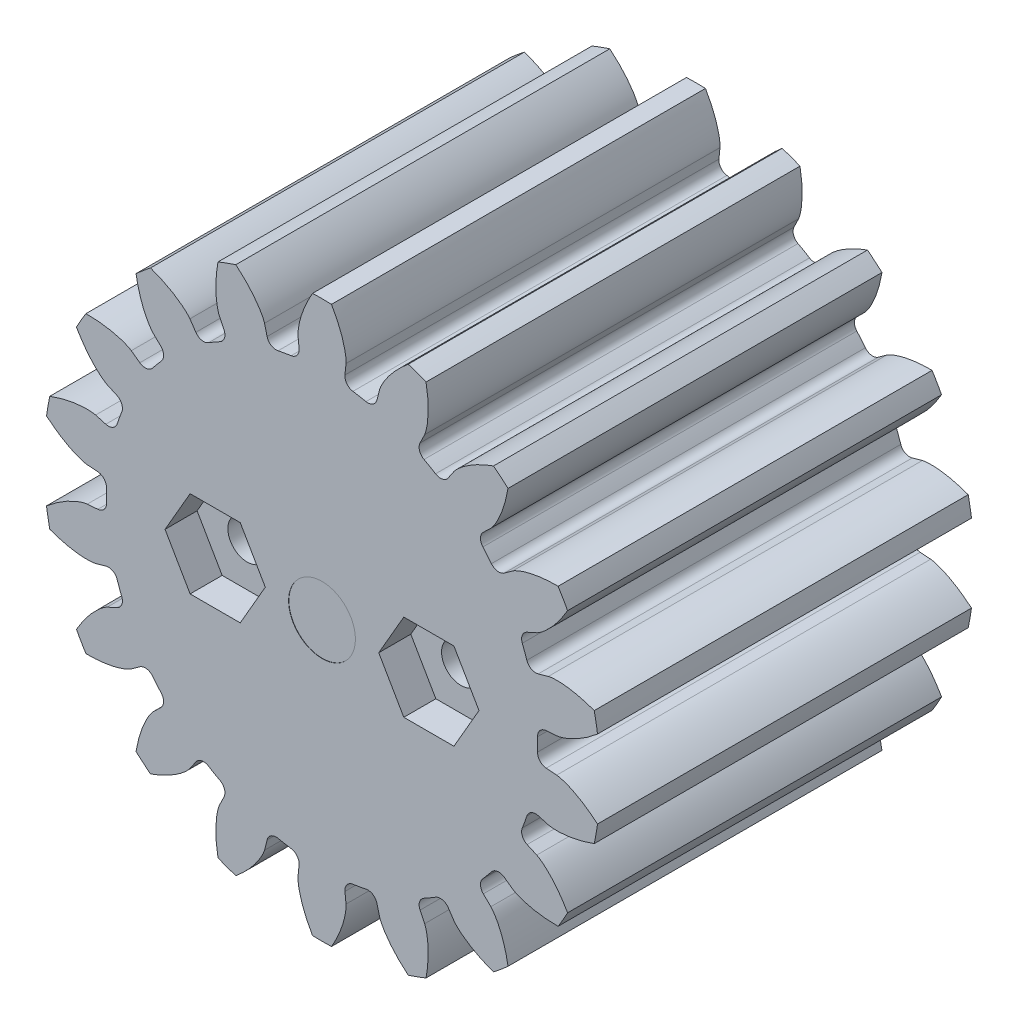
SolidWorks part; units mm, degrees
ref_plane "Front Plane" through (0, 0, 0) normal (0, 0, 1) x (1, 0, 0)
ref_plane "Top Plane" through (0, 0, 0) normal (0, 1, 0) x (1, 0, 0)
ref_plane "Right Plane" through (0, 0, 0) normal (1, 0, 0) x (0, 0, -1)
sketch "Sketch1" plane through (0, 0, 0) normal (0, 0, 1) x (1, 0, 0)
  line L0 (0, 0) -> (0, 9.525) construction
  line L1 (-3.0613, 10.6392) -> (3.0613, 8.4108) construction
  circle A0 centre (0, 0) radius 8.2021 construction
  circle A1 centre (0, 0) radius 10.5833 construction
  circle A2 centre (0, 0) radius 9.525 construction
  circle A3 centre (0, 0) radius 8.9506 construction
  circle A4 centre (0, 0) radius 2.3813 construction
  circle A5 centre (0, 0) radius 6.858 construction
  point P8 (304.8, 0)
  point P13 (228.6, 0)
  dimension "OD | Outside Diameter" = 21.1667
  dimension "Root Diameter" = 16.4042
  dimension "Gear Pitch Diameter" = 19.05
  dimension "Base Diameter" = 17.9011
  dimension "For Shaft Diameter" = 4.7625
  dimension "Hub Diameter" = 13.716
  dimension "Pressure Angle" = 20
  dimension "Number of Teeth" = 457.2
  dimension "Gear Pitch | Diametral Pitch" = 609.6
sketch "Sketch2" plane through (0, 0, 0) normal (1, 0, 0) x (0, 0, -1)
  line L0 (-6.35, 0) -> (6.35, 0) construction
  line L1 (-6.35, 10.5833) -> (6.35, 10.5833) construction
  point P2 (0, 10.5833)
  point P4 (0, 0)
  point P6 (0, 10.5833)
  dimension "Overall Width" = 12.7
  dimension "Hub Width" = 6.35
  dimension "Face Width" = 6.35
sketch "Sketch3" plane through (0, 0, 0) normal (0, 0, 1) x (1, 0, 0)
  circle A0 centre (0, 0) radius 10.5833
  circle A1 centre (0, 0) radius 10.5833 construction
extrude "Boss-Extrude1" add sketch "Sketch3" against normal blind 15.24
sketch "Sketch4" plane through (0, 0, 0) normal (0, 0, 1) x (1, 0, 0)
  line L0 (0, 0) -> (8.1806, 0.593) construction
  line L2 (0, 0) -> (8.1806, -0.593) construction
  line L4 (8.1806, 0.593) -> (8.9271, 0.6471)
  line L5 (8.9271, -0.6471) -> (8.1806, -0.593)
  arc A0 (8.1806, 0.593) -> (8.1806, -0.593) centre (0, 0) cw
  arc A3 (10.4791, 1.4815) -> (10.4791, -1.4815) centre (0, 0) cw
  circle A4 centre (0, 0) radius 10.5833 construction
  spline S0 degree 4 poles (8.9271, 0.6471) (8.9298, 0.6473) (8.9371, 0.6481) (8.951, 0.6499) (8.9735, 0.6535) (9.0022, 0.659) (9.039, 0.6671) (9.0823, 0.6779) (9.1296, 0.6912) (9.1807, 0.7071) (9.2315, 0.7243) (9.2819, 0.7426) (9.3319, 0.762) (9.3922, 0.7867) (9.464, 0.8182) (9.5473, 0.8575) (9.6409, 0.905) (9.7354, 0.9567) (9.8276, 1.0102) (9.9198, 1.0673) (10.0083, 1.1246) (10.0992, 1.1871) (10.1825, 1.2464) (10.2747, 1.3161) (10.3487, 1.3734) (10.4449, 1.4524) (10.5013, 1.5001) (10.5668, 1.5571) (10.5956, 1.5831) (10.6134, 1.599) knots 0 0 0 0 0 0.005377 0.015084 0.028532 0.04661 0.064855 0.092111 0.119476 0.146842 0.174209 0.201575 0.228941 0.256307 0.307035 0.361767 0.4165 0.471232 0.525964 0.580697 0.635429 0.690161 0.744894 0.799626 0.854358 0.909091 0.954545 1 1 1 1 1 construction
  spline S1 degree 4 poles (8.9271, 0.6471) (8.9298, 0.6473) (8.9371, 0.6481) (8.951, 0.6499) (8.9735, 0.6535) (9.0022, 0.659) (9.039, 0.6671) (9.0823, 0.6779) (9.1296, 0.6912) (9.1807, 0.7071) (9.2315, 0.7243) (9.2819, 0.7426) (9.3319, 0.762) (9.3922, 0.7867) (9.464, 0.8182) (9.5473, 0.8575) (9.6409, 0.905) (9.7354, 0.9567) (9.8276, 1.0102) (9.9198, 1.0673) (10.0083, 1.1246) (10.0992, 1.1871) (10.1825, 1.2464) (10.2747, 1.3161) (10.3487, 1.3734) (10.424, 1.4353) (10.4605, 1.4658) (10.4791, 1.4815) knots 0 0 0 0 0 0.005377 0.015084 0.028532 0.04661 0.064855 0.092111 0.119476 0.146842 0.174209 0.201575 0.228941 0.256307 0.307035 0.361767 0.4165 0.471232 0.525964 0.580697 0.635429 0.690161 0.744894 0.799626 0.854358 0.909091 0.909091 0.909091 0.909091 0.909091
  spline S2 degree 4 poles (8.9271, -0.6471) (8.9298, -0.6473) (8.9371, -0.6481) (8.951, -0.6499) (8.9735, -0.6535) (9.0022, -0.659) (9.039, -0.6671) (9.0823, -0.6779) (9.1296, -0.6912) (9.1807, -0.7071) (9.2315, -0.7243) (9.2819, -0.7426) (9.3319, -0.762) (9.3922, -0.7867) (9.464, -0.8182) (9.5473, -0.8575) (9.6409, -0.905) (9.7354, -0.9567) (9.8276, -1.0102) (9.9198, -1.0673) (10.0083, -1.1246) (10.0992, -1.1871) (10.1825, -1.2464) (10.2747, -1.3161) (10.3487, -1.3734) (10.4449, -1.4524) (10.5013, -1.5001) (10.5668, -1.5571) (10.5956, -1.5831) (10.6134, -1.599) knots 0 0 0 0 0 0.005377 0.015084 0.028532 0.04661 0.064855 0.092111 0.119476 0.146842 0.174209 0.201575 0.228941 0.256307 0.307035 0.361767 0.4165 0.471232 0.525964 0.580697 0.635429 0.690161 0.744894 0.799626 0.854358 0.909091 0.954545 1 1 1 1 1 construction
  spline S3 degree 4 poles (8.9271, -0.6471) (8.9298, -0.6473) (8.9371, -0.6481) (8.951, -0.6499) (8.9735, -0.6535) (9.0022, -0.659) (9.039, -0.6671) (9.0823, -0.6779) (9.1296, -0.6912) (9.1807, -0.7071) (9.2315, -0.7243) (9.2819, -0.7426) (9.3319, -0.762) (9.3922, -0.7867) (9.464, -0.8182) (9.5473, -0.8575) (9.6409, -0.905) (9.7354, -0.9567) (9.8276, -1.0102) (9.9198, -1.0673) (10.0083, -1.1246) (10.0992, -1.1871) (10.1825, -1.2464) (10.2747, -1.3161) (10.3487, -1.3734) (10.424, -1.4353) (10.4605, -1.4658) (10.4791, -1.4815) knots 0 0 0 0 0 0.005377 0.015084 0.028532 0.04661 0.064855 0.092111 0.119476 0.146842 0.174209 0.201575 0.228941 0.256307 0.307035 0.361767 0.4165 0.471232 0.525964 0.580697 0.635429 0.690161 0.744894 0.799626 0.854358 0.909091 0.909091 0.909091 0.909091 0.909091
  dimension "D1" = 16.4042
extrude "Cut-Extrude1" cut sketch "Sketch4" against normal through all both and the other way through all
fillet "Fillet1" radius 0.3551 2 edges at (8.1806, -0.593, -7.62) (8.1806, 0.593, -7.62)
pattern_circular "CirPattern1" count 18 over 360 about axis through (0, 0, 6.35) along (0, 0, -1) of "Cut-Extrude1", "Fillet1"
scale "Scale3" scale about origin uniform scaling yes scale factor 2.5
sketch "Sketch10" plane through (0, 0, 0) normal (0, 0, 1) x (1, 0, 0)
  circle A0 centre (0, 0) radius 3.175
  dimension "D1" = 6.35
extrude "Cut-Extrude4" cut sketch "Sketch10" against normal blind 0.0254
sketch "Sketch11" plane through (0, 0, -38.1) normal (0, 0, -1) x (-1, 0, 0)
  circle A0 centre (0, 0) radius 3.048
  dimension "D1" = 6.096
extrude "Cut-Extrude5" cut sketch "Sketch11" against normal blind 8.636
sketch "Sketch12" plane through (0, 0, -38.1) normal (0, 0, -1) x (-1, 0, 0)
  circle A0 centre (0, 0) radius 19.05
  dimension "D1" = 38.1
sketch "Sketch13" plane through (0, 0, 0) normal (0, 0, 1) x (1, 0, 0)
  line L0 (0, 0) -> (-0.0634, 10.6281) construction
  line L1 (-5.394, 0) -> (-7.777, 4.1275)
  line L2 (-7.777, 4.1275) -> (-12.543, 4.1275)
  line L3 (-12.543, 4.1275) -> (-14.926, 0)
  line L4 (-14.926, 0) -> (-12.543, -4.1275)
  line L5 (-12.543, -4.1275) -> (-7.777, -4.1275)
  line L6 (-7.777, -4.1275) -> (-5.394, 0)
  line L7 (14.926, 0) -> (12.543, 4.1275)
  line L8 (12.543, 4.1275) -> (7.777, 4.1275)
  line L9 (7.777, 4.1275) -> (5.394, 0)
  line L10 (5.394, 0) -> (7.777, -4.1275)
  line L11 (7.777, -4.1275) -> (12.543, -4.1275)
  line L12 (12.543, -4.1275) -> (14.926, 0)
  circle A0 centre (-10.16, 0) radius 4.1275 construction
  circle A1 centre (10.16, 0) radius 4.1275 construction
  dimension "D1" = 8.255
  dimension "D2" = 8.255
  dimension "D3" = 10.16
  dimension "D4" = 10.16
extrude "Cut-Extrude6" cut sketch "Sketch13" against normal blind 3.048
sketch "Sketch14" plane through (0, 0, -3.048) normal (0, 0, 1) x (1, 0, 0)
  line L0 (-7.777, 4.1275) -> (-12.543, 4.1275) construction
  line L1 (12.543, 4.1275) -> (7.777, 4.1275) construction
  circle A0 centre (-10.16, 0) radius 1.8415
  circle A1 centre (10.16, 0) radius 1.8415
  point P6 (-10.16, 4.1275)
  point P9 (10.16, 4.1275)
  dimension "D1" = 3.683
  dimension "D2" = 3.683
extrude "Cut-Extrude7" cut sketch "Sketch14" against normal blind 12.7
sketch "Sketch15" plane through (0, 0, -38.1) normal (0, 0, -1) x (-1, 0, 0)
  circle A0 centre (0, 0) radius 29.3442
  circle A1 centre (0, 0) radius 8.89
  dimension "D1" = 17.78
extrude "Cut-Extrude8" cut sketch "Sketch15" against normal blind 2.54
equation "\"Root Diameter@Sketch1\"=\"Root Diameter\""
equation "\"OD | Outside Diameter@Sketch1\"=\"Outside Diameter\""
equation "\"D1@CirPattern1\"=\"Number of Teeth\""
equation "\"Diametral Pitch\"= 24"
equation "\"Number of Teeth\"= 18"
equation "\"Pressure Angle\"=20"
equation "\"Pitch Diameter\"= \"Number of Teeth\" / \"Diametral Pitch\""
equation "\"Base Diameter\"= \"Pitch Diameter\" * cos ( \"Pressure Angle\" )"
equation "\"Outside Diameter\"= ( \"Number of Teeth\" + 2 ) / \"Diametral Pitch\""
equation "\"Dedendum\"= 1.25 / \"Diametral Pitch\""
equation "\"Root Diameter\"= \"Pitch Diameter\" - ( 2 * \"Dedendum\" )"
equation "\"Pitch Angle\"= 360deg / \"Number of Teeth\""
equation "\"Alpha\"= sqr ( \"Pitch Diameter\" ^ 2 - \"Base Diameter\" ^ 2 ) / \"Base Diameter\" * 180 / PI - \"Pressure Angle\""
equation "\"Beta\"= ( \"Pitch Angle\" / 4 - \"Alpha\" )"
equation "\"Phi\"= sqr ( ( \"Outside Diameter\" / 2 ) ^ 2 - ( \"Base Diameter\" / 2 ) ^ 2 ) / ( \"Base Diameter\" / 2 )"
equation "\"Addendum\"= 1 / \"Diametral Pitch\""
equation "\"WorkingDepth\"= 2 / \"Diametral Pitch\""
equation "\"WholeDepth\"= 2.25 / \"Diametral Pitch\""
equation "\"Clearance\"= 0.25 / \"Diametral Pitch\""
equation "\"ToothThickness\"= ( pi * 2 ) / \"Diametral Pitch\""
equation "\"CircularPitch\"= pi / \"Diametral Pitch\""
equation "\"Number of Teeth@Sketch1\"=\"Number of Teeth\""
equation "\"Gear Pitch | Diametral Pitch@Sketch1\"=\"Diametral Pitch\""
equation "\"Pressure Angle@Sketch1\"=\"Pressure Angle\""
equation "\"Gear Pitch Diameter@Sketch1\"=\"Pitch Diameter\""
equation "\"Base Diameter@Sketch1\"=\"Base Diameter\""
equation "\"Fillet\"= \"Clearance\" * cos ( \"Pressure Angle\" ) * tan ( ( 90 + \"Pressure Angle\" ) / 2 )"
equation "\"D1@Fillet1\"=\"Fillet\""
equation "\"D1@Sketch4\"=if( \"Base Diameter\">\"Root Diameter\",\"Root Diameter\",\"Base Diameter\"-.00001)"
equation "\"D1@Fillet2\"=\"Fillet\""
